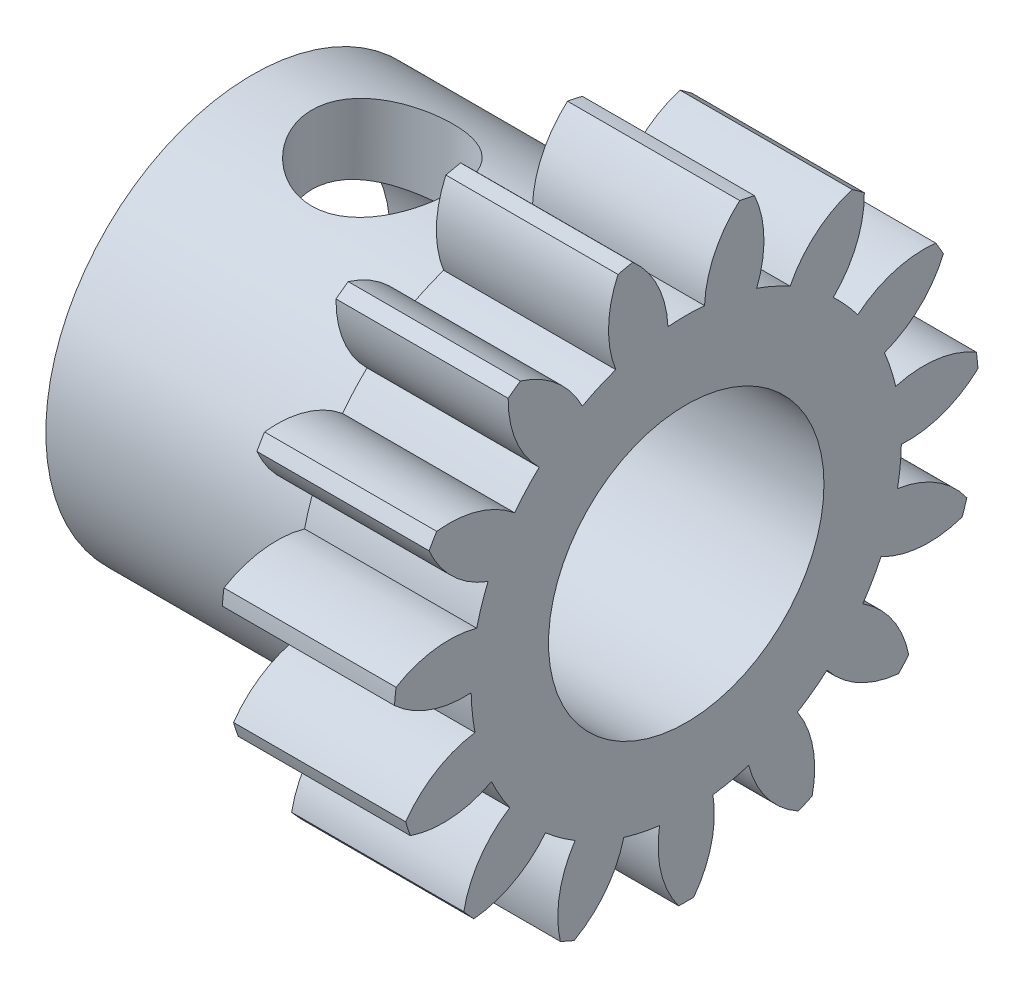
SolidWorks part; units mm, degrees
material "Plain Carbon Steel"
ref_plane "Front Plane" through (0, 0, 0) normal (0, 0, 1) x (1, 0, 0)
ref_plane "Top Plane" through (0, 0, 0) normal (0, 1, 0) x (1, 0, 0)
ref_plane "Right Plane" through (0, 0, 0) normal (1, 0, 0) x (0, 0, -1)
ref_plane "Plane1" through (0, 0, 0) normal (0, 0, -1) x (-1, 0, 0)
sketch "Sketch1" plane through (0, 0, 0) normal (0, 0, -1) x (-1, 0, 0)
  line L0 (-2.5, 4.25) -> (-2.5, 0)
  line L1 (-2.5, 0) -> (0, 0)
  line L2 (0, 0) -> (0, 4.25)
  line L3 (0, 4.25) -> (-2.5, 4.25)
  line L4 (-2.5, 0) -> (0, 0) construction
revolve "Revolve1" add sketch "Sketch1" angle 360 about L4
sketch "Sketch2" plane through (2.5, 0, 0) normal (1, 0, 0) x (0, 0, -1)
  arc A0 (2.586, 3.3727) -> (2.1353, 2.2803) centre (1.0861, 3.3523) cw
  arc A1 (2.1353, 2.2803) -> (2.491, 1.8853) centre (0, 0) cw
  arc A2 (2.491, 1.8853) -> (3.6245, 2.2193) centre (3.4475, 0.7298) cw
  arc A3 (3.6245, 2.2193) -> (2.586, 3.3727) centre (0, 0) ccw
extrude "Cut-Extrude1" cut sketch "Sketch2" against normal through all
sketch "Sketch3" plane through (2.5, 0, 0) normal (1, 0, 0) x (0, 0, -1)
  arc A0 (3.7342, 2.0293) -> (2.8782, 1.2146) centre (2.3557, 2.6207) cw
  arc A1 (2.8782, 1.2146) -> (3.0425, 0.7091) centre (0, 0) cw
  arc A2 (3.0425, 0.7091) -> (4.2138, 0.5532) centre (3.4462, -0.7355) cw
  arc A3 (4.2138, 0.5532) -> (3.7342, 2.0293) centre (0, 0) ccw
extrude "Cut-Extrude2" cut sketch "Sketch3" against normal through all
sketch "Sketch4" plane through (2.5, 0, 0) normal (1, 0, 0) x (0, 0, -1)
  arc A0 (4.2368, 0.335) -> (3.1234, -0.0611) centre (3.218, 1.436) cw
  arc A1 (3.1234, -0.0611) -> (3.0678, -0.5897) centre (0, 0) cw
  arc A2 (3.0678, -0.5897) -> (4.0745, -1.2086) centre (2.8491, -2.0736) cw
  arc A3 (4.0745, -1.2086) -> (4.2368, 0.335) centre (0, 0) ccw
extrude "Cut-Extrude3" cut sketch "Sketch4" against normal through all
sketch "Sketch5" plane through (2.5, 0, 0) normal (1, 0, 0) x (0, 0, -1)
  arc A0 (4.0067, -1.4172) -> (2.8285, -1.3262) centre (3.5238, 0.0029) cw
  arc A1 (2.8285, -1.3262) -> (2.5628, -1.7865) centre (0, 0) cw
  arc A2 (2.5628, -1.7865) -> (3.2307, -2.7613) centre (1.7594, -3.0532) cw
  arc A3 (3.2307, -2.7613) -> (4.0067, -1.4172) centre (0, 0) ccw
extrude "Cut-Extrude4" cut sketch "Sketch5" against normal through all
sketch "Sketch6" plane through (2.5, 0, 0) normal (1, 0, 0) x (0, 0, -1)
  arc A0 (3.0839, -2.9244) -> (2.0446, -2.362) centre (3.2204, -1.4306) cw
  arc A1 (2.0446, -2.362) -> (1.6146, -2.6744) centre (0, 0) cw
  arc A2 (1.6146, -2.6744) -> (1.8283, -3.8367) centre (0.3654, -3.5048) cw
  arc A3 (1.8283, -3.8367) -> (3.0839, -2.9244) centre (0, 0) ccw
extrude "Cut-Extrude5" cut sketch "Sketch6" against normal through all
sketch "Sketch7" plane through (2.5, 0, 0) normal (1, 0, 0) x (0, 0, -1)
  arc A0 (1.6279, -3.9259) -> (0.9071, -2.9894) centre (2.3601, -2.6168) cw
  arc A1 (0.9071, -2.9894) -> (0.3872, -3.0999) centre (0, 0) cw
  arc A2 (0.3872, -3.0999) -> (0.1097, -4.2486) centre (-1.0917, -3.3505) cw
  arc A3 (0.1097, -4.2486) -> (1.6279, -3.9259) centre (0, 0) ccw
extrude "Cut-Extrude6" cut sketch "Sketch7" against normal through all
sketch "Sketch8" plane through (2.5, 0, 0) normal (1, 0, 0) x (0, 0, -1)
  arc A0 (-0.1097, -4.2486) -> (-0.3872, -3.0999) centre (1.0917, -3.3505) cw
  arc A1 (-0.3872, -3.0999) -> (-0.9071, -2.9894) centre (0, 0) cw
  arc A2 (-0.9071, -2.9894) -> (-1.6279, -3.9259) centre (-2.3601, -2.6168) cw
  arc A3 (-1.6279, -3.9259) -> (-0.1097, -4.2486) centre (0, 0) ccw
extrude "Cut-Extrude7" cut sketch "Sketch8" against normal through all
sketch "Sketch9" plane through (2.5, 0, 0) normal (1, 0, 0) x (0, 0, -1)
  arc A0 (-1.8283, -3.8367) -> (-1.6146, -2.6744) centre (-0.3654, -3.5048) cw
  arc A1 (-1.6146, -2.6744) -> (-2.0446, -2.362) centre (0, 0) cw
  arc A2 (-2.0446, -2.362) -> (-3.0839, -2.9244) centre (-3.2204, -1.4306) cw
  arc A3 (-3.0839, -2.9244) -> (-1.8283, -3.8367) centre (0, 0) ccw
extrude "Cut-Extrude8" cut sketch "Sketch9" against normal through all
sketch "Sketch10" plane through (2.5, 0, 0) normal (1, 0, 0) x (0, 0, -1)
  arc A0 (-3.2307, -2.7613) -> (-2.5628, -1.7865) centre (-1.7594, -3.0532) cw
  arc A1 (-2.5628, -1.7865) -> (-2.8285, -1.3262) centre (0, 0) cw
  arc A2 (-2.8285, -1.3262) -> (-4.0067, -1.4172) centre (-3.5238, 0.0029) cw
  arc A3 (-4.0067, -1.4172) -> (-3.2307, -2.7613) centre (0, 0) ccw
extrude "Cut-Extrude9" cut sketch "Sketch10" against normal through all
sketch "Sketch11" plane through (2.5, 0, 0) normal (1, 0, 0) x (0, 0, -1)
  arc A0 (-4.0745, -1.2086) -> (-3.0678, -0.5897) centre (-2.8491, -2.0736) cw
  arc A1 (-3.0678, -0.5897) -> (-3.1234, -0.0611) centre (0, 0) cw
  arc A2 (-3.1234, -0.0611) -> (-4.2368, 0.335) centre (-3.218, 1.436) cw
  arc A3 (-4.2368, 0.335) -> (-4.0745, -1.2086) centre (0, 0) ccw
extrude "Cut-Extrude10" cut sketch "Sketch11" against normal through all
sketch "Sketch12" plane through (2.5, 0, 0) normal (1, 0, 0) x (0, 0, -1)
  arc A0 (-4.2138, 0.5532) -> (-3.0425, 0.7091) centre (-3.4462, -0.7355) cw
  arc A1 (-3.0425, 0.7091) -> (-2.8782, 1.2146) centre (0, 0) cw
  arc A2 (-2.8782, 1.2146) -> (-3.7342, 2.0293) centre (-2.3557, 2.6207) cw
  arc A3 (-3.7342, 2.0293) -> (-4.2138, 0.5532) centre (0, 0) ccw
extrude "Cut-Extrude11" cut sketch "Sketch12" against normal through all
sketch "Sketch13" plane through (2.5, 0, 0) normal (1, 0, 0) x (0, 0, -1)
  arc A0 (-2.586, 3.3727) -> (-3.6245, 2.2193) centre (0, 0) ccw
  arc A1 (-3.6245, 2.2193) -> (-2.491, 1.8853) centre (-3.4475, 0.7298) cw
  arc A2 (-2.491, 1.8853) -> (-2.1353, 2.2803) centre (0, 0) cw
  arc A3 (-2.1353, 2.2803) -> (-2.586, 3.3727) centre (-1.0861, 3.3523) cw
extrude "Cut-Extrude12" cut sketch "Sketch13" against normal through all
sketch "Sketch14" plane through (2.5, 0, 0) normal (1, 0, 0) x (0, 0, -1)
  arc A0 (-0.9906, 4.1329) -> (-2.4085, 3.5016) centre (0, 0) ccw
  arc A1 (-2.4085, 3.5016) -> (-1.5088, 2.7355) centre (-2.8526, 2.0689) cw
  arc A2 (-1.5088, 2.7355) -> (-1.0232, 2.9517) centre (0, 0) cw
  arc A3 (-1.0232, 2.9517) -> (-0.9906, 4.1329) centre (0.3713, 3.5042) cw
extrude "Cut-Extrude13" cut sketch "Sketch14" against normal through all
sketch "Sketch15" plane through (2.5, 0, 0) normal (1, 0, 0) x (0, 0, -1)
  arc A0 (-0.776, 4.1785) -> (-0.2658, 3.1127) centre (-1.7645, 3.0503) cw
  arc A1 (-0.2658, 3.1127) -> (0.2658, 3.1127) centre (0, 0) cw
  arc A2 (0.2658, 3.1127) -> (0.776, 4.1785) centre (1.7645, 3.0503) cw
  arc A3 (0.776, 4.1785) -> (-0.776, 4.1785) centre (0, 0) ccw
extrude "Cut-Extrude14" cut sketch "Sketch15" against normal through all
sketch "Sketch16" plane through (2.5, 0, 0) normal (1, 0, 0) x (0, 0, -1)
  arc A0 (0.9906, 4.1329) -> (1.0232, 2.9517) centre (-0.3713, 3.5042) cw
  arc A1 (1.0232, 2.9517) -> (1.5088, 2.7355) centre (0, 0) cw
  arc A2 (1.5088, 2.7355) -> (2.4085, 3.5016) centre (2.8526, 2.0689) cw
  arc A3 (2.4085, 3.5016) -> (0.9906, 4.1329) centre (0, 0) ccw
extrude "Cut-Extrude15" cut sketch "Sketch16" against normal through all
sketch "Sketch17" plane through (0, 0, 0) normal (0, 0, 1) x (1, 0, 0)
  line L0 (-3.8001, 3) -> (-3.8001, 0)
  line L1 (-3.8001, 0) -> (0, 0)
  line L2 (0, 0) -> (0, 3)
  line L3 (0, 3) -> (-3.8001, 3)
  line L4 (-3.8001, 0) -> (0, 0) construction
revolve "Revolve2" add sketch "Sketch17" angle 360 about L4
hole_wizard "Ø4.0 (4) Diameter Hole1" positions "Sketch19" profile "Sketch18" hole size "Ø4.0" standard "ANSI Metric"
sketch "Sketch19" plane through (2.5, 0, 0) normal (1, 0, 0) x (0, 0, -1)
  point P0 (0, 0)
sketch "Sketch18" plane through (2.5, 0, 0) normal (0, 1, 0) x (0, 0, -1)
  line L0 (0, 0) -> (0, 6.3001)
  line L1 (0, 6.3001) -> (2, 6.3001)
  line L2 (2, 6.3001) -> (2, 0)
  line L5 (2, 0) -> (0, 0)
  line L11 (0, -6.35) -> (0, 107.95) construction
  dimension "Thru Hole Dia." = 4
  dimension "Thru Hole Depth" = 6.3001
hole_wizard "Tap Drill for M2.5x0.45 Tap1" positions "3DSketch1" profile "Sketch20" hole size "M2.5x0.45" standard "ANSI Metric"
sketch3d "3DSketch1"
  point P0 (-1.9001, 3, 0.0133)
sketch "Sketch20" plane through (-1.9001, 3, 0.0133) normal (1, 0, 0) x (0, -0.0044, 1)
  line L0 (0, 0) -> (0, 6)
  line L1 (0, 6) -> (1.025, 6)
  line L2 (1.025, 6) -> (1.025, 0)
  line L5 (1.025, 0) -> (0, 0)
  line L10 (0, 6) -> (-1.025, 6) construction
  line L11 (0, -6.35) -> (0, 107.95) construction
  dimension "Hole Dia." = 2.05
  dimension "Hole Depth" = 6
  dimension "Drill Angle" = 180
